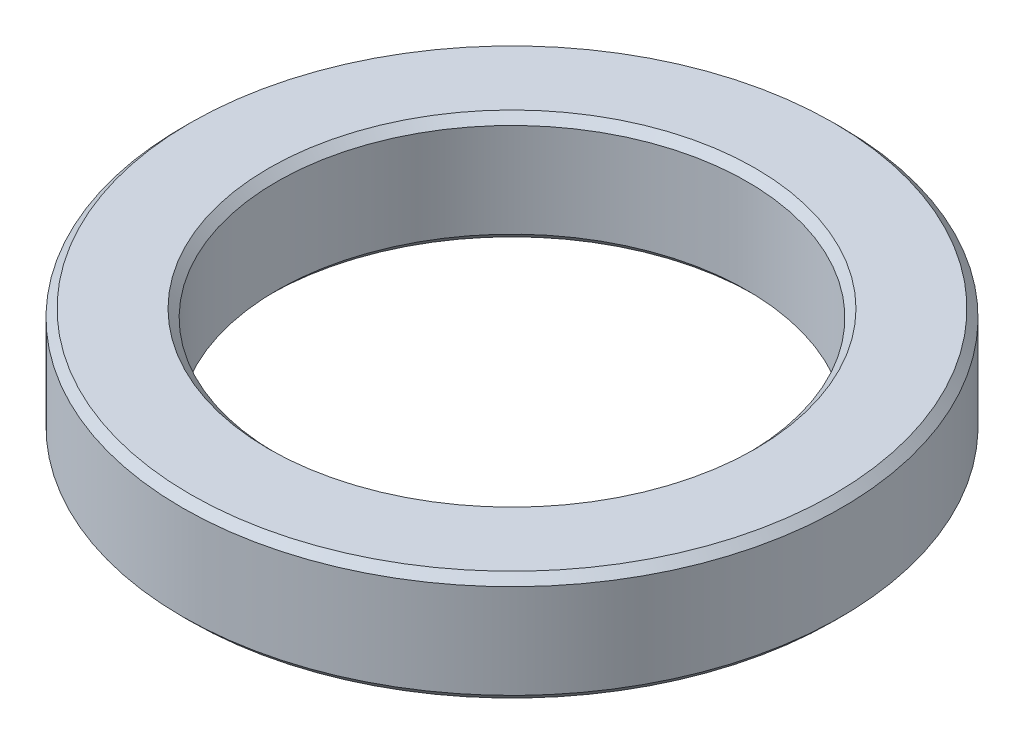
SolidWorks part; units mm, degrees
material "AISI 321 退火不锈钢 (SS)"
ref_plane "前视基准面" through (0, 0, 0) normal (0, 0, 1) x (1, 0, 0)
ref_plane "上视基准面" through (0, 0, 0) normal (0, 1, 0) x (1, 0, 0)
ref_plane "右视基准面" through (0, 0, 0) normal (1, 0, 0) x (0, 0, -1)
sketch "草图1" plane through (0, 0, 0) normal (0, 1, 0) x (1, 0, 0)
  circle A0 centre (0, 0) radius 21
  circle A1 centre (0, 0) radius 15
  dimension "D1" = 42
  dimension "D2" = 30
extrude "凸台-拉伸1" add sketch "草图1" along normal blind 7
chamfer "倒角1" distance 0.5 angle 45 4 edges at (0, 0, 15) (0, 7, 15) (0, 0, 21) (0, 7, 21)
